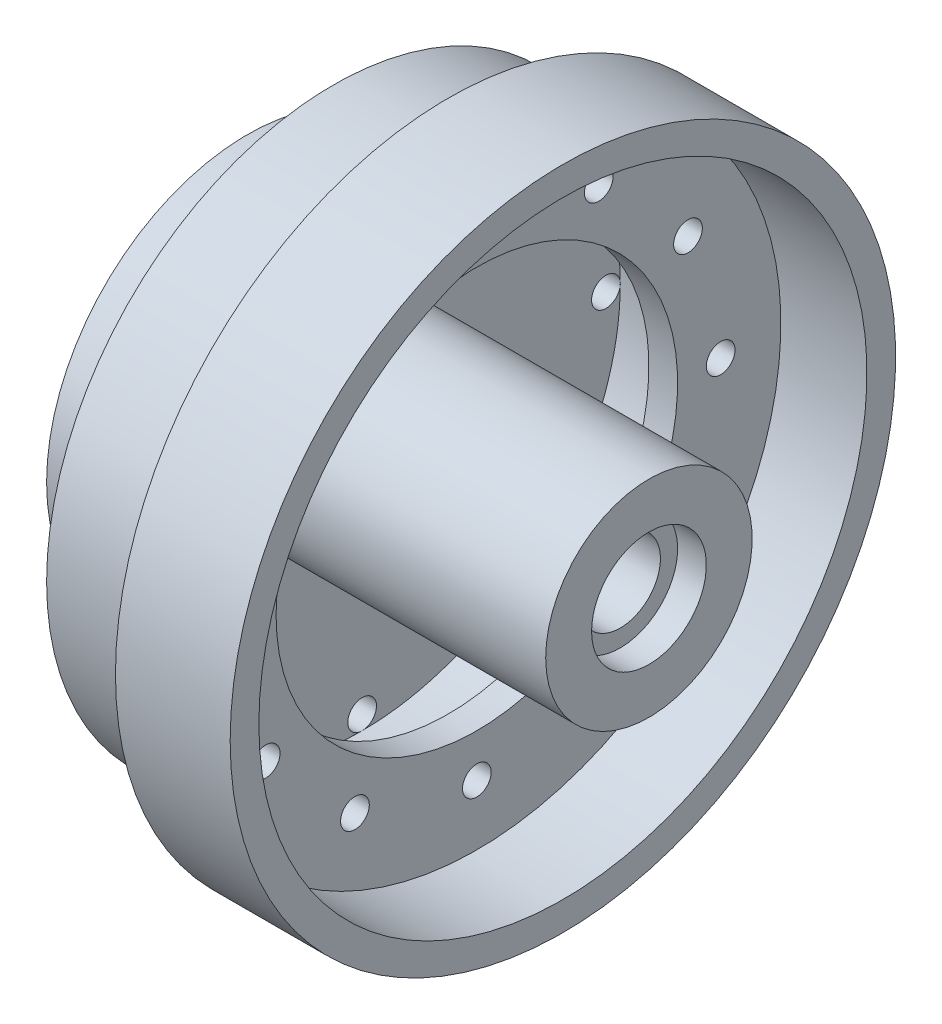
SolidWorks part; units mm, degrees
ref_plane "Piano frontale" through (0, 0, 0) normal (0, 0, 1) x (1, 0, 0)
ref_plane "Piano superiore" through (0, 0, 0) normal (0, 1, 0) x (1, 0, 0)
ref_plane "Piano destro" through (0, 0, 0) normal (1, 0, 0) x (0, 0, -1)
sketch "Schizzo1" plane through (0, 0, 0) normal (0, 0, 1) x (1, 0, 0)
  line L0 (-35, 7) -> (45, 7)
  line L3 (50, 10) -> (50, 18)
  line L4 (50, 18) -> (0.003, 18)
  line L5 (0.003, 18) -> (0.003, 45)
  line L6 (0.003, 45) -> (15, 45)
  line L7 (15, 45) -> (15, 35)
  line L8 (15, 35) -> (20, 35)
  line L9 (20, 35) -> (20, 53)
  line L10 (20, 53) -> (35, 53)
  line L11 (35, 53) -> (35, 58)
  line L12 (35, 58) -> (15, 58)
  line L13 (15, 58) -> (15, 50)
  line L14 (15, 50) -> (-5, 50)
  line L15 (-5, 50) -> (-5, 35)
  line L16 (-5, 35) -> (-20, 35)
  line L17 (-20, 35) -> (-20, 30)
  line L18 (-20, 30) -> (-5, 30)
  line L19 (-5, 30) -> (-5, 18)
  line L21 (-35, 7) -> (-35, 13)
  line L22 (-35, 13) -> (-5, 18)
  line L23 (46.75, 0) -> (-46.75, 0) construction
  line L24 (50, 10) -> (45, 10)
  line L25 (45, 10) -> (45, 7)
  line L27 (0, -28.05) -> (0, 28.05) construction
  line L28 (-44.9398, 0) -> (78.9955, 0) construction
  point P27 (35, 55.5)
  dimension "D2" = 58
  dimension "D3" = 5
  dimension "D4" = 5
  dimension "D5" = 35
  dimension "D6" = 45
  dimension "D7" = 5
  dimension "D8" = 5.003
  dimension "D9" = 70
  dimension "D10" = 55
  dimension "D11" = 40
  dimension "D12" = 13
  dimension "D13" = 7
  dimension "D14" = 15
  dimension "D15" = 18
  dimension "D16" = 10
  dimension "D17" = 35
  dimension "D18" = 5
  dimension "D19" = 5
  dimension "D20" = 20
  dimension "D21" = 35
  dimension "D22" = 5
revolve "Rivoluzione1" add sketch "Schizzo1" angle 360 about L28
sketch "Schizzo2" plane through (-5, 0, 0) normal (-1, 0, 0) x (0, 0, 1)
  circle A1 centre (0, 0) radius 42.5 construction
  circle A2 centre (0, -42.5) radius 2.5
  dimension "D1" = 85
  dimension "D2" = 5
extrude "Taglio-Estrusione1" cut sketch "Schizzo2" against normal through all
pattern_circular "RipetizioneCircolare1" count 12 over 360 about axis through (0, 0, 0) along (1, 0, 0) of "Taglio-Estrusione1"
